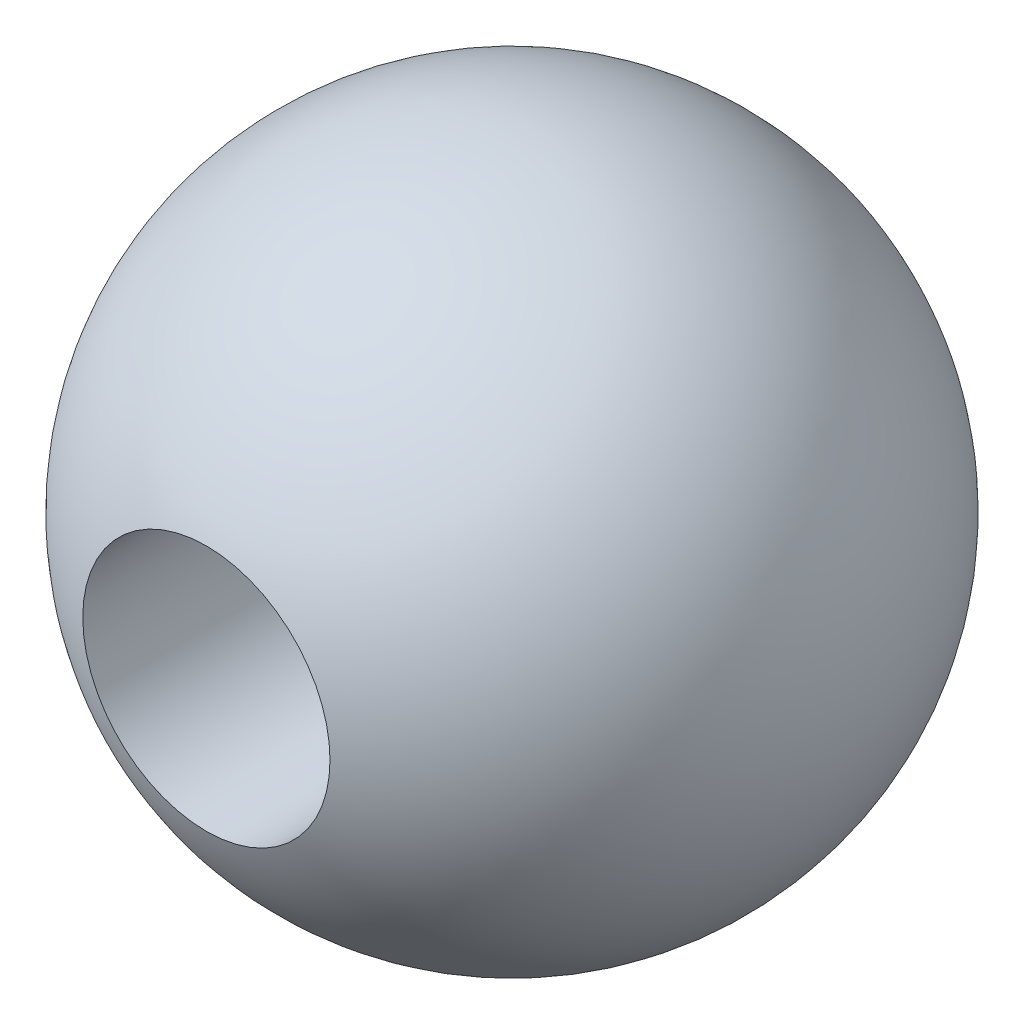
SolidWorks part; units mm, degrees
ref_plane "Front Plane" through (0, 0, 0) normal (0, 0, 1) x (1, 0, 0)
ref_plane "Top Plane" through (0, 0, 0) normal (0, 1, 0) x (1, 0, 0)
ref_plane "Right Plane" through (0, 0, 0) normal (1, 0, 0) x (0, 0, -1)
sketch "Sketch1" plane through (0, 0, 0) normal (0, 0, 1) x (1, 0, 0)
  line L0 (0, 1) -> (0, -1) construction
  line L1 (0, 1) -> (0, -1)
  arc A0 (0, 1) -> (0, -1) centre (0, 0) ccw
  dimension "D1" = 1
revolve "Revolve1" add sketch "Sketch1" angle 360 about L0
ref_plane "Plane1" through (0, 0, 1) normal (0, 0, 1) x (1, 0, 0)
sketch "Sketch2" plane through (0, 0, 1) normal (0, 0, 1) x (1, 0, 0)
  circle A0 centre (0, 0) radius 0.375
  dimension "D1" = 0.75
extrude "Cut-Extrude1" cut sketch "Sketch2" against normal blind 0.68
